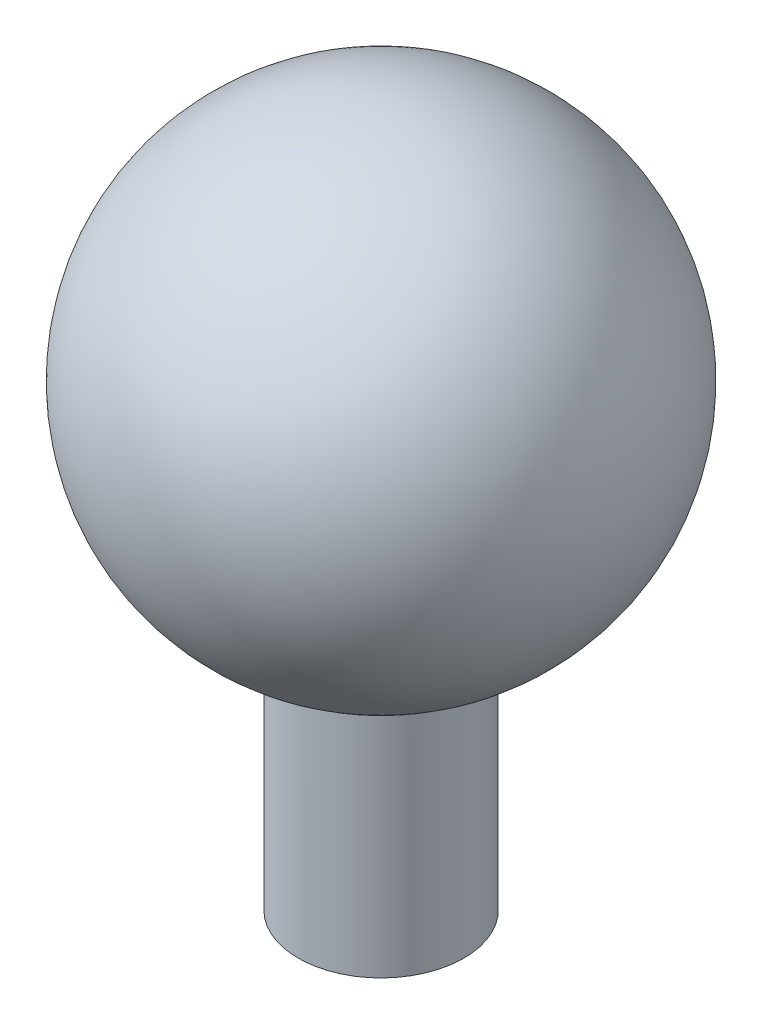
SolidWorks part; units mm, degrees
ref_plane "前视基准面" through (0, 0, 0) normal (0, 0, 1) x (1, 0, 0)
ref_plane "上视基准面" through (0, 0, 0) normal (0, 1, 0) x (1, 0, 0)
ref_plane "右视基准面" through (0, 0, 0) normal (1, 0, 0) x (0, 0, -1)
other "Configuration Table"
sketch "草图1" plane through (0, 0, 0) normal (0, 0, 1) x (1, 0, 0)
  line L0 (0, 0) -> (-7, 0)
  line L1 (-7, 0) -> (-7, 20)
  line L2 (0, -55) -> (0, 55) construction
  line L4 (0, 0) -> (7, 0)
  line L5 (0, 0) -> (0, 58.735)
  arc A0 (0, 58.735) -> (-7, 20) centre (0, 38.735) ccw
  dimension "D1" = 40
  dimension "D2" = 7
  dimension "D3" = 20
revolve "旋转1" add sketch "草图1" angle 360 about L5
sketch "草图2" plane through (0, 0, 0) normal (0, -1, 0) x (1, 0, 0)
  circle A0 centre (0, 0) radius 3
  dimension "D1" = 6
extrude "切除-拉伸1" cut sketch "草图2" against normal blind 48
